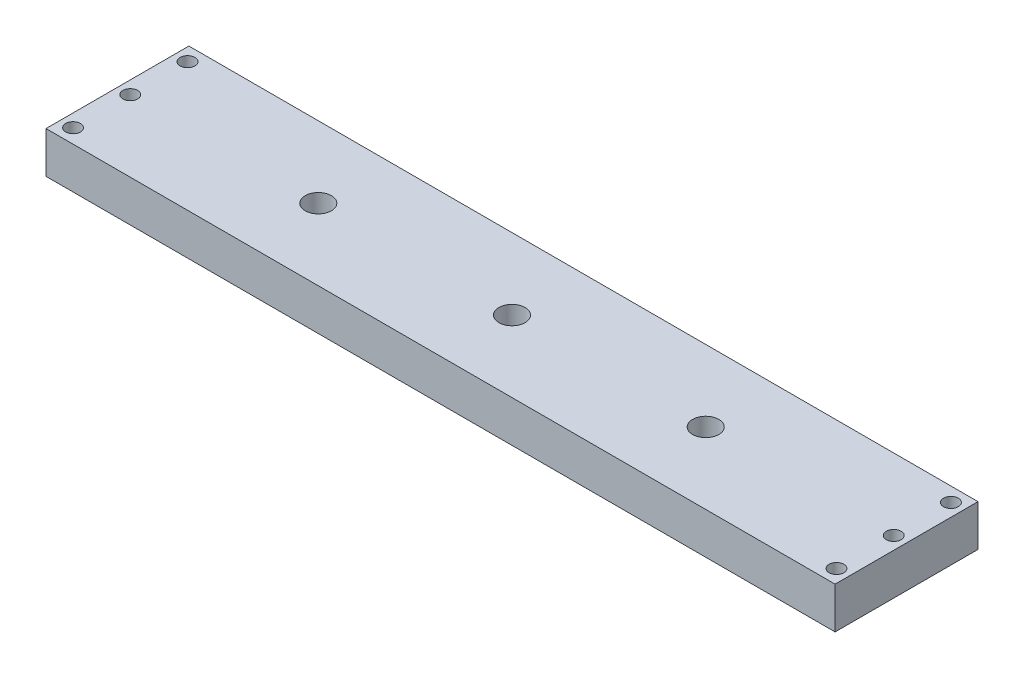
SolidWorks part; units mm, degrees
ref_plane "Front Plane" through (0, 0, 0) normal (0, 0, 1) x (1, 0, 0)
ref_plane "Top Plane" through (0, 0, 0) normal (0, 1, 0) x (1, 0, 0)
ref_plane "Right Plane" through (0, 0, 0) normal (1, 0, 0) x (0, 0, -1)
sketch "Sketch1" plane through (0, 0, 0) normal (0, 1, 0) x (1, 0, 0)
  line L1 (-101.6, -18.3998) -> (101.6, -18.3998)
  line L2 (-101.6, -18.3998) -> (-101.6, 18.3998)
  line L3 (-101.6, 18.3998) -> (101.6, 18.3998)
  line L4 (101.6, -18.3998) -> (101.6, 18.3998)
  line L5 (-101.6, -18.3998) -> (101.6, 18.3998) construction
  line L6 (-101.6, 18.3998) -> (101.6, -18.3998) construction
  point P0 (0, 0)
  dimension "D1" = 203.2
  dimension "D2" = 36.7995
extrude "Boss-Extrude1" add sketch "Sketch1" along normal blind 10.668
sketch "Sketch3" plane through (0, 0, 0) normal (0, -1, 0) x (1, 0, 0)
  line L0 (-101.6, 0) -> (-60.6691, 0) construction
  line L1 (-101.6, -18.3998) -> (-101.6, 18.3998) construction
  line L2 (-98.298, 18.3998) -> (-98.298, -18.3998) construction
  line L3 (-101.6, 18.3998) -> (101.6, 18.3998) construction
  line L4 (101.6, -18.3998) -> (-101.6, -18.3998) construction
  circle A0 centre (-98.298, 14.732) radius 1.905
  circle A1 centre (-98.298, 0) radius 1.905
  circle A2 centre (-98.298, -14.732) radius 1.905
  point P15 (0, 0)
  point P18 (0, 0)
  point P19 (0, 0)
  point P20 (0, 0)
  point P21 (0, 0)
  dimension "D2" = 3.81
  dimension "D3" = 3.81
  dimension "D5" = 3.81
  dimension "D1" = 14.732
  dimension "D4" = 3.302
  dimension "D6" = 14.732
extrude "Cut-Extrude1" cut sketch "Sketch3" against normal through all
mirror "Mirror1" about plane through (0, 0, 0) normal (1, 0, 0) of "Cut-Extrude1"
sketch "Sketch4" plane through (0, 10.668, 0) normal (0, 1, 0) x (1, 0, 0)
  line L0 (3.3782, 0) -> (96.393, 0) construction
  line L1 (0, 18.3998) -> (0, -18.3998) construction
  line L2 (101.6, 18.3998) -> (-101.6, 18.3998) construction
  line L3 (-101.6, -18.3998) -> (101.6, -18.3998) construction
  circle A0 centre (-49.8856, 0) radius 3.3782
  circle A2 centre (0, 0) radius 3.3782
  circle A3 centre (49.8856, 0) radius 3.3782
  circle A4 centre (98.298, 0) radius 1.905 construction
  point P13 (49.8856, 0)
  dimension "D1" = 6.7564
  dimension "D2" = 6.7564
extrude "Cut-Extrude2" cut sketch "Sketch4" against normal through all
